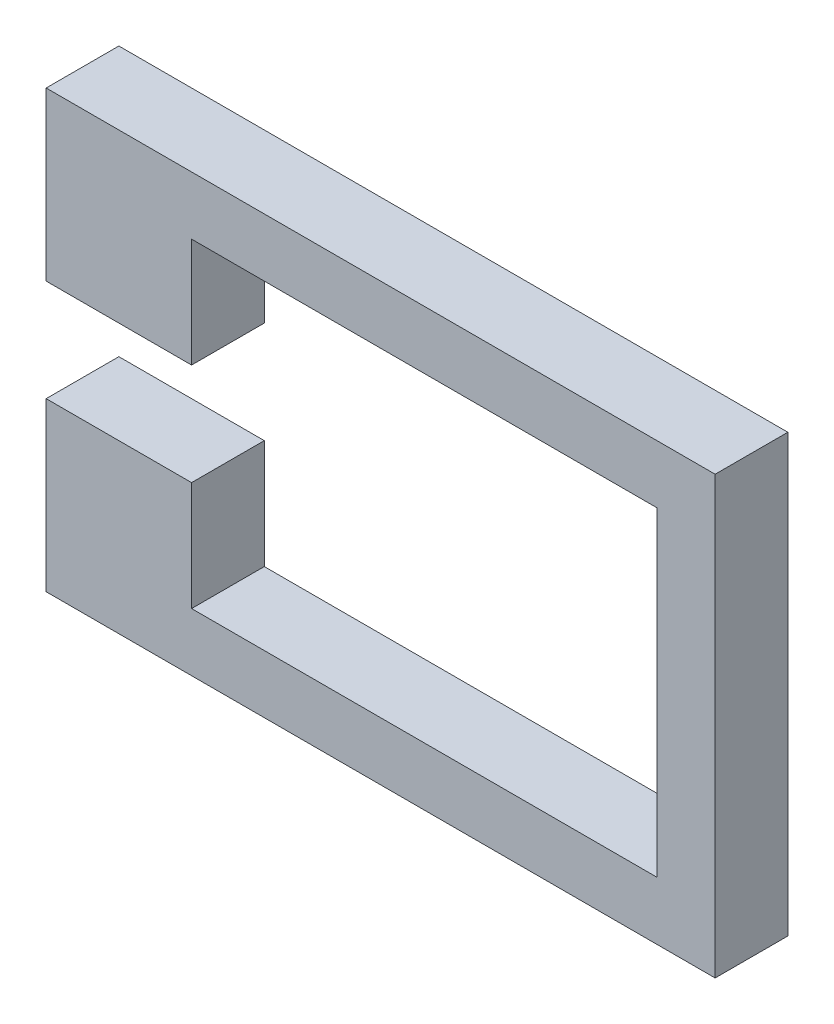
SolidWorks part; units mm, degrees
ref_plane "Front Plane" through (0, 0, 0) normal (0, 0, 1) x (1, 0, 0)
ref_plane "Top Plane" through (0, 0, 0) normal (0, 1, 0) x (1, 0, 0)
ref_plane "Right Plane" through (0, 0, 0) normal (1, 0, 0) x (0, 0, -1)
sketch "Sketch1" plane through (0, 0, 0) normal (0, 0, 1) x (1, 0, 0)
  line L0 (-13.97, -8.255) -> (-26.67, -8.255)
  line L1 (31.75, -31.75) -> (-26.67, -31.75)
  line L2 (31.75, -31.75) -> (31.75, 6.35)
  line L3 (31.75, 6.35) -> (-26.67, 6.35)
  line L4 (-26.67, -31.75) -> (-26.67, -17.145)
  line L5 (0, 0) -> (-1.27, 1.27) construction
  line L6 (1.27, 1.27) -> (0, 0) construction
  line L7 (26.67, -26.67) -> (-13.97, -26.67)
  line L8 (26.67, -26.67) -> (26.67, 1.27)
  line L9 (26.67, 1.27) -> (-13.97, 1.27)
  line L10 (-13.97, -26.67) -> (-13.97, -17.145)
  line L11 (-13.97, -17.145) -> (-26.67, -17.145)
  line L15 (-26.67, -8.255) -> (-26.67, 6.35)
  line L19 (-13.97, -8.255) -> (-13.97, 1.27)
  point P0 (0, 0)
  point P10 (-13.97, -12.7)
  dimension "D1" = 58.42
  dimension "D2" = 5.08
  dimension "D3" = 5.08
  dimension "D4" = 40.64
  dimension "D5" = 27.94
  dimension "D6" = 8.89
  dimension "D8" = 38.1
extrude "Boss-Extrude1" add sketch "Sketch1" along normal blind 6.35
